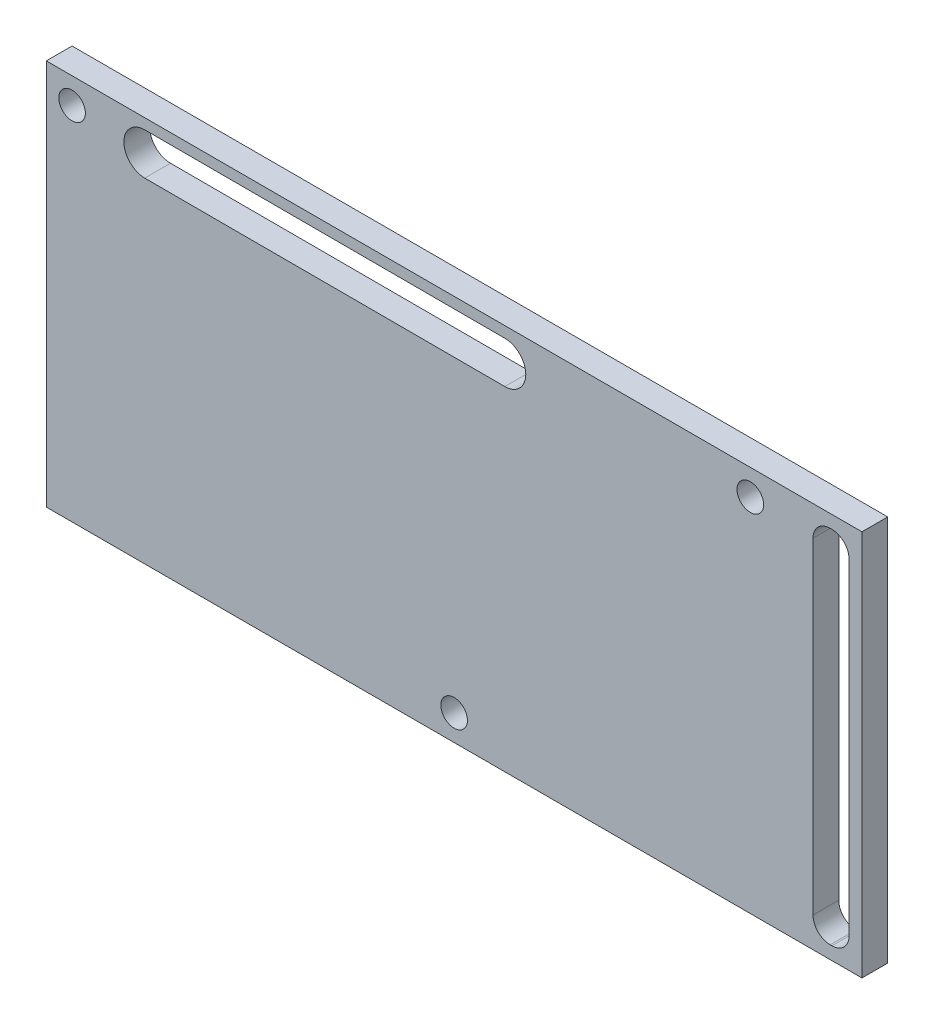
SolidWorks part; units mm, degrees
ref_plane "Front Plane" through (0, 0, 0) normal (0, 0, 1) x (1, 0, 0)
ref_plane "Top Plane" through (0, 0, 0) normal (0, 1, 0) x (1, 0, 0)
ref_plane "Right Plane" through (0, 0, 0) normal (1, 0, 0) x (0, 0, -1)
sketch "Sketch4" plane through (0, 0, 0) normal (0, 0, 1) x (1, 0, 0)
  line L0 (55.7407, 57.1248) -> (-39.2593, 57.1248)
  line L1 (55.7407, 12.1158) -> (55.7407, 57.1248)
  line L2 (-39.2593, 12.1158) -> (55.7407, 12.1158)
  line L3 (-39.2593, 57.1248) -> (-39.2593, 12.1158)
  line L4 (-11.3421, 32.1248) -> (13.6579, 32.1248) construction
  line L9 (5.6579, 37.1248) -> (21.6579, 37.1248) construction
  line L10 (3.6579, 35.1248) -> (3.6579, 29.1248) construction
  line L11 (5.6579, 27.1248) -> (21.6579, 27.1248) construction
  line L12 (23.6579, 35.1248) -> (23.6579, 29.1248) construction
  line L13 (3.6579, 37.1248) -> (23.6579, 27.1248) construction
  line L14 (3.6579, 27.1248) -> (23.6579, 37.1248) construction
  line L15 (13.6579, 32.1248) -> (38.6579, 32.1248) construction
  line L16 (14.1507, 53.4127) -> (-27.7852, 53.4692) construction
  line L17 (52.0407, 55.6248) -> (52.2407, 55.6248)
  line L18 (50.0407, 53.6248) -> (50.0407, 15.6158)
  line L19 (52.0407, 13.6158) -> (52.2407, 13.6158)
  line L20 (54.2407, 53.6248) -> (54.2407, 15.6158)
  line L21 (14.1475, 50.9772) -> (-27.7885, 51.0338)
  line L22 (14.154, 55.8481) -> (-27.7819, 55.9047)
  circle A0 centre (42.7407, 54.1248) radius 1.55
  circle A1 centre (38.6579, 32.1248) radius 1.6 construction
  circle A3 centre (-11.3421, 32.1248) radius 1.6 construction
  arc A5 (5.6579, 37.1248) -> (3.6579, 35.1248) centre (5.6579, 35.1248) ccw construction
  circle A7 centre (8.2407, 15.1158) radius 1.55
  circle A8 centre (-36.2593, 54.1248) radius 1.55
  arc A9 (21.6579, 37.1248) -> (23.6579, 35.1248) centre (21.6579, 35.1248) cw construction
  arc A10 (5.6579, 27.1248) -> (3.6579, 29.1248) centre (5.6579, 29.1248) cw construction
  arc A11 (21.6579, 27.1248) -> (23.6579, 29.1248) centre (21.6579, 29.1248) ccw construction
  arc A12 (52.0407, 55.6248) -> (50.0407, 53.6248) centre (52.0407, 53.6248) ccw
  arc A13 (52.2407, 55.6248) -> (54.2407, 53.6248) centre (52.2407, 53.6248) cw
  arc A14 (52.0407, 13.6158) -> (50.0407, 15.6158) centre (52.0407, 15.6158) cw
  arc A15 (52.2407, 13.6158) -> (54.2407, 15.6158) centre (52.2407, 15.6158) ccw
  arc A16 (14.1475, 50.9772) -> (14.154, 55.8481) centre (14.1507, 53.4127) ccw
  arc A17 (-27.7819, 55.9047) -> (-27.7885, 51.0338) centre (-27.7852, 53.4692) ccw
  point P0 (13.6579, 32.1248)
  point P42 (50.0407, 13.6158)
  point P45 (54.2407, 13.6158)
  point P50 (-6.8172, 53.441)
  dimension "D3" = 50
  dimension "D17" = 2
  dimension "D18" = 2
  dimension "D19" = 2
  dimension "D20" = 2
  dimension "D21" = 2
  dimension "D22" = 2
  dimension "D23" = 2
  dimension "D24" = 2
  dimension "D1" = 95
  dimension "D2" = 45.009
  dimension "D4" = 25
  dimension "D5" = 3
  dimension "D6" = 3
  dimension "D7" = 3
  dimension "D8" = 1.5
  dimension "D9" = 3
  dimension "D10" = 47.5
  dimension "D11" = 82
  dimension "D12" = 1.5
  dimension "D13" = 1.5
  dimension "D14" = 4.2
  dimension "D15" = 20
  dimension "D16" = 10
extrude "Boss-Extrude6" add sketch "Sketch4" along normal blind 3
